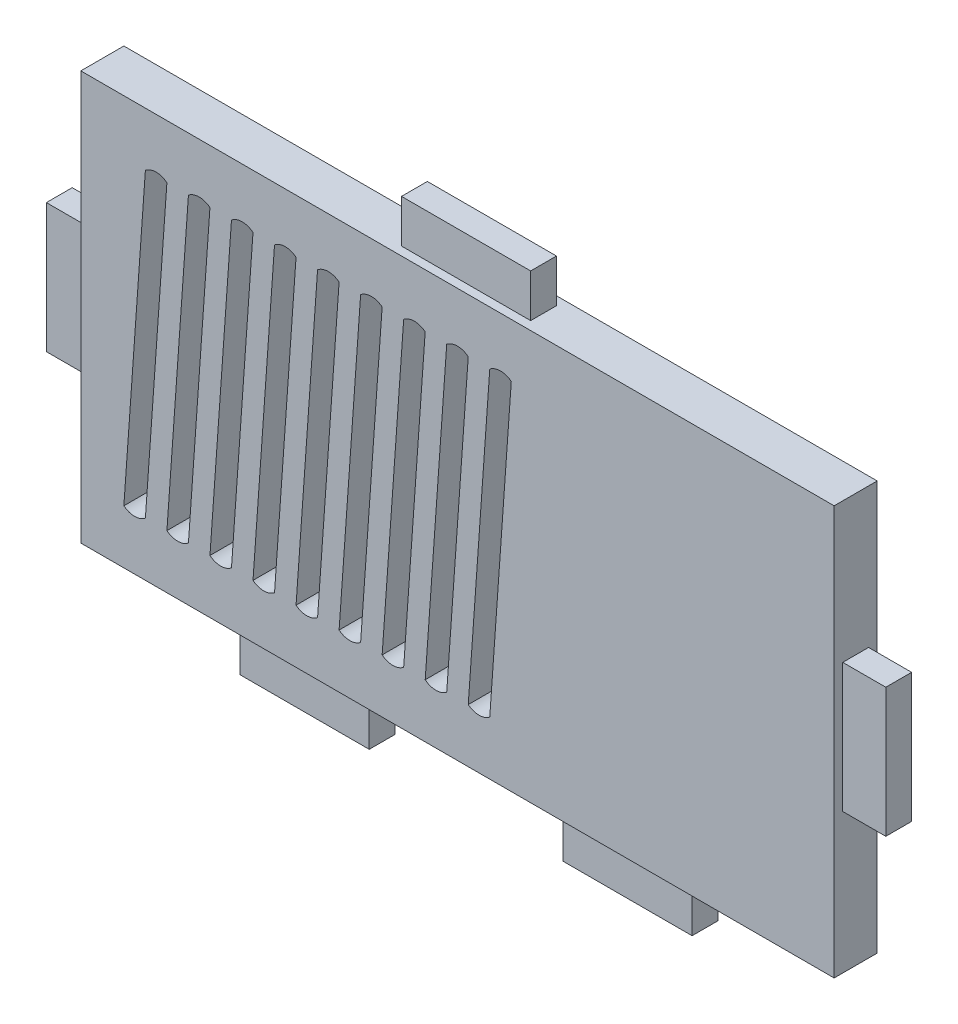
SolidWorks part; units mm, degrees
ref_plane "Plano frontal" through (0, 0, 0) normal (0, 0, 1) x (1, 0, 0)
ref_plane "Plano superior" through (0, 0, 0) normal (0, 1, 0) x (1, 0, 0)
ref_plane "Plano direito" through (0, 0, 0) normal (1, 0, 0) x (0, 0, -1)
sketch "Esboço1" plane through (0, 0, 0) normal (0, 0, 1) x (1, 0, 0)
  line L1 (87.5, -47.5) -> (-87.5, -47.5)
  line L2 (87.5, -47.5) -> (87.5, 47.5)
  line L3 (87.5, 47.5) -> (-87.5, 47.5)
  line L4 (-87.5, -47.5) -> (-87.5, 47.5)
  line L5 (87.5, -47.5) -> (-87.5, 47.5) construction
  line L6 (87.5, 47.5) -> (-87.5, -47.5) construction
  point P0 (0, 0)
  dimension "D1" = 95
  dimension "D2" = 175
extrude "Ressalto-extrusão1" add sketch "Esboço1" along normal blind 10
sketch "Esboço2" plane through (-87.5, 0, 0) normal (-1, 0, 0) x (0, 0, 1)
  line L0 (5, 47.5) -> (5, -47.5) construction
  line L1 (10, 47.5) -> (0, 47.5) construction
  line L2 (10, -47.5) -> (0, -47.5) construction
  line L3 (10, 0) -> (0, 0) construction
  line L4 (10, 47.5) -> (10, -47.5) construction
  line L6 (8, -15) -> (2, -15)
  line L7 (8, -15) -> (8, 15)
  line L8 (8, 15) -> (2, 15)
  line L9 (2, -15) -> (2, 15)
  line L10 (8, -15) -> (2, 15) construction
  line L11 (8, 15) -> (2, -15) construction
  point P11 (5, 0)
  dimension "D1" = 30
  dimension "D2" = 6
extrude "Ressalto-extrusão2" add sketch "Esboço2" along normal blind 10
sketch "Esboço3" plane through (87.5, 0, 0) normal (1, 0, 0) x (0, 0, -1)
  line L0 (-5, 50.9763) -> (-5, -49.5797) construction
  line L1 (0, 0) -> (-10, 0) construction
  line L2 (-10, -47.5) -> (-10, 47.5) construction
  line L4 (-8, -15) -> (-2, -15)
  line L5 (-8, -15) -> (-8, 15)
  line L6 (-8, 15) -> (-2, 15)
  line L7 (-2, -15) -> (-2, 15)
  line L8 (-8, -15) -> (-2, 15) construction
  line L9 (-8, 15) -> (-2, -15) construction
  point P7 (-5, 0)
  dimension "D1" = 6
  dimension "D2" = 30
extrude "Ressalto-extrusão3" add sketch "Esboço3" along normal blind 10
sketch "Esboço4" plane through (0, -47.5, 0) normal (0, -1, 0) x (1, 0, 0)
  line L0 (-87.5, 5) -> (87.5, 5) construction
  line L1 (-87.5, 10) -> (-87.5, 0) construction
  line L2 (87.5, 8) -> (87.5, 2) construction
  line L3 (0, 10) -> (0, 0) construction
  line L4 (-87.5, 10) -> (87.5, 10) construction
  line L5 (22.5, 8) -> (52.5, 8)
  line L6 (-22.5, 2) -> (-52.5, 2)
  line L7 (-22.5, 2) -> (-22.5, 8)
  line L8 (-22.5, 8) -> (-52.5, 8)
  line L9 (-52.5, 2) -> (-52.5, 8)
  line L10 (-22.5, 2) -> (-52.5, 8) construction
  line L11 (-22.5, 8) -> (-52.5, 2) construction
  line L12 (52.5, 2) -> (52.5, 8)
  line L13 (22.5, 2) -> (52.5, 2)
  line L14 (22.5, 2) -> (22.5, 8)
  point P11 (-37.5, 5)
  dimension "D1" = 30
  dimension "D2" = 6
  dimension "D3" = 50
extrude "Ressalto-extrusão4" add sketch "Esboço4" along normal blind 10
sketch "Esboço5" plane through (0, 47.5, 0) normal (0, 1, 0) x (1, 0, 0)
  line L0 (0, 0) -> (0, -10) construction
  line L1 (87.5, -10) -> (-87.5, -10) construction
  line L2 (-87.5, -5) -> (87.5, -5) construction
  line L3 (-87.5, -10) -> (-87.5, 0) construction
  line L4 (87.5, -10) -> (87.5, 0) construction
  line L6 (15, -8) -> (-15, -8)
  line L7 (15, -8) -> (15, -2)
  line L8 (15, -2) -> (-15, -2)
  line L9 (-15, -8) -> (-15, -2)
  line L10 (15, -8) -> (-15, -2) construction
  line L11 (15, -2) -> (-15, -8) construction
  point P11 (0, -5)
  dimension "D1" = 30
  dimension "D2" = 6
extrude "Ressalto-extrusão5" add sketch "Esboço5" along normal blind 10
sketch "Esboço6" plane through (0, 0, 10) normal (0, 0, 1) x (1, 0, 0)
  line L0 (-125.3171, 0) -> (134.5998, 0) construction
  line L1 (-87.5, 47.5) -> (-87.5, -47.5) construction
  line L2 (-77.5, -35) -> (32.5, -35) construction
  line L3 (-77.5, -35) -> (-77.5, 35) construction
  line L4 (-77.5, 35) -> (32.5, 35) construction
  line L5 (32.5, -35) -> (32.5, 35) construction
  line L6 (-77.5, -35) -> (32.5, 35) construction
  line L7 (-77.5, 35) -> (32.5, -35) construction
  line L8 (-72.5, 35) -> (-72.5, -35) construction
  line L9 (-67.5, 35) -> (-67.5, -35) construction
  line L10 (-77.5, -35) -> (-72.5, 35)
  line L11 (-72.5, -35) -> (-67.5, 35)
  line L12 (-62.5, -35) -> (-57.5, 35)
  line L13 (-67.5, -35) -> (-62.5, 35)
  line L14 (-52.5, -35) -> (-47.5, 35)
  line L15 (-57.5, -35) -> (-52.5, 35)
  line L16 (-42.5, -35) -> (-37.5, 35)
  line L17 (-47.5, -35) -> (-42.5, 35)
  line L18 (-32.5, -35) -> (-27.5, 35)
  line L19 (-37.5, -35) -> (-32.5, 35)
  line L20 (-22.5, -35) -> (-17.5, 35)
  line L21 (-27.5, -35) -> (-22.5, 35)
  line L22 (-12.5, -35) -> (-7.5, 35)
  line L23 (-17.5, -35) -> (-12.5, 35)
  line L24 (-2.5, -35) -> (2.5, 35)
  line L25 (-7.5, -35) -> (-2.5, 35)
  line L26 (7.5, -35) -> (12.5, 35)
  line L27 (2.5, -35) -> (7.5, 35)
  line L32 (27.5, -35) -> (32.5, 35) [skipped]
  line L33 (22.5, -35) -> (27.5, 35) [skipped]
  line L34 (17.5, -35) -> (22.5, 35) [skipped]
  line L35 (12.5, -35) -> (17.5, 35) [skipped]
  arc A0 (-72.5, 35) -> (-67.5, 35) centre (-70, 31.8775) cw
  arc A1 (-77.5, -35) -> (-72.5, -35) centre (-75, -31.8775) ccw
  arc A2 (-62.5, 35) -> (-57.5, 35) centre (-60, 31.8775) cw
  arc A3 (-67.5, -35) -> (-62.5, -35) centre (-65, -31.8775) ccw
  arc A4 (-52.5, 35) -> (-47.5, 35) centre (-50, 31.8775) cw
  arc A5 (-57.5, -35) -> (-52.5, -35) centre (-55, -31.8775) ccw
  arc A6 (-42.5, 35) -> (-37.5, 35) centre (-40, 31.8775) cw
  arc A7 (-47.5, -35) -> (-42.5, -35) centre (-45, -31.8775) ccw
  arc A8 (-32.5, 35) -> (-27.5, 35) centre (-30, 31.8775) cw
  arc A9 (-37.5, -35) -> (-32.5, -35) centre (-35, -31.8775) ccw
  arc A10 (-22.5, 35) -> (-17.5, 35) centre (-20, 31.8775) cw
  arc A11 (-27.5, -35) -> (-22.5, -35) centre (-25, -31.8775) ccw
  arc A12 (-12.5, 35) -> (-7.5, 35) centre (-10, 31.8775) cw
  arc A13 (-17.5, -35) -> (-12.5, -35) centre (-15, -31.8775) ccw
  arc A14 (-2.5, 35) -> (2.5, 35) centre (0, 31.8775) cw
  arc A15 (-7.5, -35) -> (-2.5, -35) centre (-5, -31.8775) ccw
  arc A16 (7.5, 35) -> (12.5, 35) centre (10, 31.8775) cw
  arc A17 (2.5, -35) -> (7.5, -35) centre (5, -31.8775) ccw
  arc A22 (27.5, 35) -> (32.5, 35) centre (30, 31.8775) cw [skipped]
  arc A23 (22.5, -35) -> (27.5, -35) centre (25, -31.8775) ccw [skipped]
  arc A24 (17.5, 35) -> (22.5, 35) centre (20, 31.8775) cw [skipped]
  arc A25 (12.5, -35) -> (17.5, -35) centre (15, -31.8775) ccw [skipped]
  point P3 (-22.5, 0)
  dimension "D6" = 4
  dimension "D7" = 4
  dimension "D1" = 110
  dimension "D2" = 10
  dimension "D3" = 70
  dimension "D4" = 5
  dimension "D5" = 5
  dimension "D8" = 11
extrude "Corte-extrusão1" cut sketch "Esboço6" against normal blind 10
